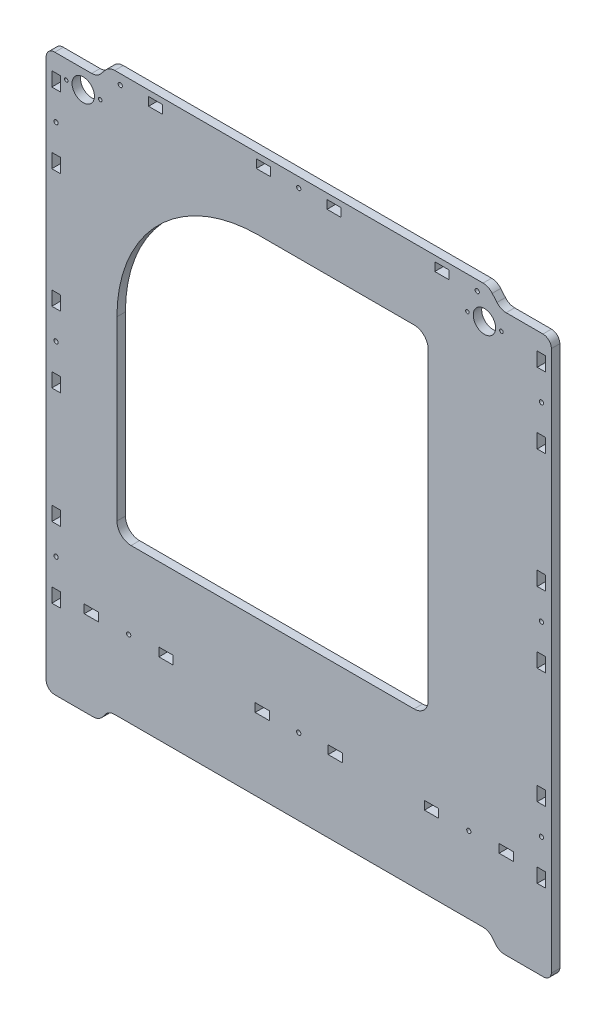
SolidWorks part; units mm, degrees
ref_plane "Спереди" through (0, 0, 0) normal (0, 0, 1) x (1, 0, 0)
ref_plane "Сверху" through (0, 0, 0) normal (0, 1, 0) x (1, 0, 0)
ref_plane "Справа" through (0, 0, 0) normal (1, 0, 0) x (0, 0, -1)
sketch "Эскиз1" plane through (0, 0, 0) normal (0, 0, 1) x (1, 0, 0)
  line L0 (146.8614, 191.5323) -> (172.8978, 191.5323)
  line L1 (-168.1958, 44.9723) -> (-168.1958, 34.9723)
  line L2 (174.8042, 34.9723) -> (168.8042, 34.9723)
  line L3 (178.8042, 185.543) -> (178.8042, -196.6758)
  line L4 (-178.1958, 185.543) -> (-178.1958, -195.7677)
  line L5 (172.8978, -201.7677) -> (145.8614, -201.7677)
  line L6 (-138.5545, -198.7314) -> (-136.2586, -195.7117)
  line L7 (-172.1022, -201.7677) -> (-145.0658, -201.7677)
  line L8 (-129.7473, -192.6754) -> (130.5428, -192.6754)
  line L9 (139.35, -198.7314) -> (137.0542, -195.7117)
  line L10 (174.8042, 179.1323) -> (174.8042, 169.359)
  line L11 (96.4442, 197.5323) -> (106.4199, 197.5323)
  line L12 (106.4199, 197.5323) -> (106.4442, 197.5149)
  line L13 (174.8042, 169.359) -> (174.8042, 169.1323)
  line L14 (137.0542, 198.496) -> (140.35, 194.5682)
  line L15 (130.5428, 201.5323) -> (-129.7473, 201.5323)
  line L16 (-136.2586, 198.4964) -> (-139.5545, 194.5686)
  line L17 (-146.0658, 191.5323) -> (-172.1022, 191.5323)
  line L18 (106.4199, 191.5323) -> (96.4442, 191.5323)
  line L19 (-168.1958, 34.9723) -> (-174.1958, 34.9723)
  line L20 (31.0942, -141.7677) -> (21.0942, -141.7677)
  line L21 (168.8042, 34.9723) -> (168.8042, 44.9723)
  line L22 (31.0942, -135.7677) -> (31.0942, -141.7677)
  line L23 (-30.4858, -135.7677) -> (-20.4858, -135.7677)
  line L24 (21.0942, -141.7677) -> (21.0942, -135.7677)
  line L25 (-20.4858, -141.7677) -> (-30.4858, -141.7677)
  line L26 (-20.4858, -135.7677) -> (-20.4858, -141.7677)
  line L27 (-168.1958, 179.1323) -> (-168.1958, 169.1323)
  line L28 (-30.4858, -141.7677) -> (-30.4858, -135.7677)
  line L29 (-174.1958, 34.9723) -> (-174.1958, 44.9723)
  line L30 (-174.1958, 44.9723) -> (-168.1958, 44.9723)
  line L31 (21.0942, -135.7677) -> (31.0942, -135.7677)
  line L32 (-174.1958, 179.1323) -> (-168.1958, 179.1323)
  line L33 (99.0942, -141.7677) -> (89.0942, -141.7677)
  line L34 (89.0942, -141.7677) -> (89.0942, -135.7677)
  line L35 (89.0942, -135.7677) -> (99.0942, -135.7677)
  line L36 (99.0942, -135.7677) -> (99.0942, -141.7677)
  line L37 (151.8942, -141.7677) -> (141.8942, -141.7677)
  line L38 (141.8942, -141.7677) -> (141.8942, -135.7677)
  line L39 (141.8942, -135.7677) -> (151.8942, -135.7677)
  line L40 (151.8942, -135.7677) -> (151.8942, -141.7677)
  line L41 (-19.6852, 191.5323) -> (-29.6852, 191.5323)
  line L42 (-29.6852, 191.5323) -> (-29.6864, 197.5323)
  line L43 (-29.6864, 197.5323) -> (-19.6864, 197.5323)
  line L44 (-19.6864, 197.5323) -> (-19.6852, 191.5323)
  line L45 (-174.1958, 119.1323) -> (-174.1958, 129.1323)
  line L46 (-141.2858, -135.7677) -> (-141.2858, -141.7677)
  line L47 (-151.2858, -135.7677) -> (-141.2858, -135.7677)
  line L48 (20.2942, 197.5323) -> (30.2942, 197.5323)
  line L49 (30.2942, 197.5323) -> (30.2942, 191.5323)
  line L50 (-141.2858, -141.7677) -> (-151.2858, -141.7677)
  line L51 (-174.1958, -5.0277) -> (-168.1958, -5.0277)
  line L52 (-174.1958, -15.0277) -> (-174.1958, -5.0277)
  line L53 (-174.1958, 169.1323) -> (-174.1958, 179.1323)
  line L54 (-168.1958, -5.0277) -> (-168.1958, -15.0277)
  line L55 (30.2942, 191.5323) -> (20.2942, 191.5323)
  line L56 (-151.2858, -141.7677) -> (-151.2858, -135.7677)
  line L57 (-168.1958, 119.1323) -> (-174.1958, 119.1323)
  line L58 (-168.1958, -15.0277) -> (-174.1958, -15.0277)
  line L59 (20.2942, 191.5323) -> (20.2942, 197.5323)
  line L60 (-168.1958, 169.1323) -> (-174.1958, 169.1323)
  line L61 (-174.1958, -86.7577) -> (-168.1958, -86.7577)
  line L62 (-174.1958, -96.7577) -> (-174.1958, -86.7577)
  line L63 (-168.1958, 129.1323) -> (-168.1958, 119.1323)
  line L64 (-174.1958, 129.1323) -> (-168.1958, 129.1323)
  line L65 (-174.1958, -136.7477) -> (-168.1958, -136.7477)
  line L66 (-174.1958, -146.7477) -> (-174.1958, -136.7477)
  line L67 (-98.4858, -141.7677) -> (-98.4858, -135.7677)
  line L68 (-98.4858, -135.7677) -> (-88.4858, -135.7677)
  line L69 (-88.4858, -135.7677) -> (-88.4858, -141.7677)
  line L70 (-168.1958, -146.7477) -> (-174.1958, -146.7477)
  line L71 (-168.1958, -136.7477) -> (-168.1958, -146.7477)
  line L72 (-168.1958, -96.7577) -> (-174.1958, -96.7577)
  line L73 (-168.1958, -86.7577) -> (-168.1958, -96.7577)
  line L74 (174.8042, -15.0277) -> (168.8042, -15.0277)
  line L75 (168.8042, -96.7577) -> (168.8042, -86.7577)
  line L76 (174.8042, -5.0277) -> (174.8042, -15.0277)
  line L77 (174.8042, -86.7577) -> (174.8042, -96.7577)
  line L78 (174.8042, -96.7577) -> (168.8042, -96.7577)
  line L79 (168.8042, -146.7477) -> (168.8042, -136.7477)
  line L80 (168.8042, -136.7477) -> (174.8042, -136.7477)
  line L81 (174.8042, -136.7477) -> (174.8042, -146.7477)
  line L82 (168.8042, -86.7577) -> (174.8042, -86.7577)
  line L83 (168.8042, 179.1323) -> (174.8042, 179.1323)
  line L84 (168.8042, 119.1323) -> (168.8042, 129.1323)
  line L85 (168.8042, 129.1323) -> (174.8042, 129.1323)
  line L86 (174.8042, 129.1323) -> (174.8042, 119.1323)
  line L87 (168.8042, 44.9723) -> (174.8042, 44.9723)
  line L88 (174.8042, 169.1323) -> (168.8042, 169.1323)
  line L89 (174.8042, 44.9723) -> (174.8042, 34.9723)
  line L90 (-95.8352, 191.5323) -> (-105.8352, 191.5323)
  line L91 (106.4442, 191.3325) -> (106.4199, 191.5323)
  line L92 (-105.8352, 191.5323) -> (-105.8364, 197.5323)
  line L93 (174.8042, 119.1323) -> (168.8042, 119.1323)
  line L94 (-105.8364, 197.5323) -> (-95.8364, 197.5323)
  line L95 (-95.8364, 197.5323) -> (-95.8352, 191.5323)
  line L96 (174.8042, -146.7477) -> (168.8042, -146.7477)
  line L97 (168.8042, 169.1323) -> (168.8042, 179.1323)
  line L98 (106.4442, 197.5149) -> (106.4442, 191.3325)
  line L99 (-88.4858, -141.7677) -> (-98.4858, -141.7677)
  line L100 (96.4442, 191.5323) -> (96.4442, 197.5323)
  line L101 (168.8042, -15.0277) -> (168.8042, -5.0277)
  line L102 (168.8042, -5.0277) -> (174.8042, -5.0277)
  line L103 (-158.5792, -141.7677) -> (201.8861, -141.7677) construction
  line L104 (-165.4171, 178.5323) -> (-136.2586, 178.5323) construction
  line L105 (112.0065, 178.5323) -> (153.0331, 178.5323) construction
  line L106 (-128.1958, -73.4677) -> (-128.1958, 51.5323)
  line L107 (-28.1958, 151.5323) -> (81.8042, 151.5323)
  line L108 (91.8042, 141.5323) -> (91.8042, -73.4677)
  line L109 (81.8042, -83.4677) -> (-118.1958, -83.4677)
  arc A0 (-172.1022, 191.5323) -> (-178.1958, 185.543) centre (-172.1958, 185.5331) ccw
  circle A1 centre (120.4942, -138.7677) radius 1.5
  circle A2 centre (0.3042, -138.7677) radius 1.5
  circle A3 centre (-119.8858, -138.7677) radius 1.5
  arc A4 (172.8978, -201.7677) -> (178.8042, -196.6758) centre (173.2588, -196.2149) ccw
  arc A5 (-129.7473, -192.6754) -> (-136.2586, -195.7117) centre (-129.7473, -201.1754) ccw
  arc A6 (139.35, -198.7314) -> (145.8614, -201.7677) centre (145.8614, -193.2677) ccw
  arc A7 (-145.0658, -201.7677) -> (-138.5545, -198.7314) centre (-145.0658, -193.2677) ccw
  arc A8 (-178.1958, -195.7677) -> (-172.1022, -201.7677) centre (-172.1958, -195.7684) ccw
  arc A9 (137.0542, -195.7117) -> (130.5428, -192.6754) centre (130.5428, -201.1754) ccw
  arc A10 (178.8042, 185.543) -> (172.8978, 191.5323) centre (172.8042, 185.5331) ccw
  arc A11 (137.0542, 198.496) -> (130.5428, 201.5323) centre (130.5428, 193.0323) ccw
  arc A12 (140.35, 194.5682) -> (146.8614, 191.5323) centre (146.861, 200.0323) ccw
  circle A13 centre (-171.1958, -116.7377) radius 1.5
  circle A14 centre (-171.1958, 14.9723) radius 1.5
  circle A15 centre (171.8042, 149.1323) radius 1.5
  circle A16 centre (126.4442, 194.5323) radius 1.5
  circle A17 centre (-151.9958, 178.5323) radius 7.9
  circle A18 centre (171.8042, -116.7377) radius 1.5
  circle A19 centre (171.8042, 14.9723) radius 1.5
  circle A20 centre (-171.1958, 149.1323) radius 1.5
  circle A21 centre (-125.8358, 194.5323) radius 1.5
  circle A22 centre (0.3042, 194.5444) radius 1.5
  circle A23 centre (131.5042, 178.5323) radius 7.9
  arc A24 (-129.7473, 201.5323) -> (-136.2586, 198.4964) centre (-129.7476, 193.0323) ccw
  arc A25 (-146.0658, 191.5323) -> (-139.5545, 194.5686) centre (-146.0658, 200.0323) ccw
  circle A26 centre (-139.9958, 178.5323) radius 1.25
  circle A27 centre (-163.9958, 178.5323) radius 1.25
  circle A28 centre (119.5042, 178.5323) radius 1.25
  circle A29 centre (143.5042, 178.5323) radius 1.25
  arc A30 (81.8042, 151.5323) -> (91.8042, 141.5323) centre (81.8042, 141.5323) cw
  arc A31 (91.8042, -73.4677) -> (81.8042, -83.4677) centre (81.8042, -73.4677) cw
  arc A32 (-118.1958, -83.4677) -> (-128.1958, -73.4677) centre (-118.1958, -73.4677) cw
  arc A33 (-128.1958, 51.5323) -> (-28.1958, 151.5323) centre (-28.1958, 51.5323) cw
  point P155 (-174.1958, 124.1323)
  point P156 (-171.1958, -146.7477)
  point P157 (106.4442, 194.4237)
  point P161 (31.0942, -138.7677)
  dimension "D119" = 2.5
  dimension "D120" = 2.5
  dimension "D121" = 12
  dimension "D122" = 12
  dimension "D123" = 2.5
  dimension "D124" = 2.5
  dimension "D125" = 12
  dimension "D126" = 12
  dimension "D1" = 357
  dimension "D2" = 403.3
  dimension "D3" = 403.3
  dimension "D4" = 23
  dimension "D5" = 26.2
  dimension "D6" = 4
  dimension "D7" = 10
  dimension "D8" = 22.4
  dimension "D9" = 10
  dimension "D10" = 7
  dimension "D11" = 20
  dimension "D12" = 20
  dimension "D13" = 10
  dimension "D14" = 74.16
  dimension "D15" = 4
  dimension "D16" = 6
  dimension "D17" = 6
  dimension "D18" = 10
  dimension "D19" = 4
  dimension "D20" = 20
  dimension "D21" = 20
  dimension "D22" = 10
  dimension "D23" = 7
  dimension "D24" = 4
  dimension "D25" = 71.73
  dimension "D26" = 4
  dimension "D27" = 10
  dimension "D28" = 19.98
  dimension "D29" = 7
  dimension "D30" = 20.01
  dimension "D31" = 10
  dimension "D32" = 55.02
  dimension "D33" = 4
  dimension "D34" = 23
  dimension "D35" = 47.3
  dimension "D36" = 10
  dimension "D37" = 12.4
  dimension "D38" = 10
  dimension "D39" = 20
  dimension "D40" = 20
  dimension "D41" = 10
  dimension "D42" = 74.16
  dimension "D43" = 10
  dimension "D44" = 6
  dimension "D45" = 6
  dimension "D46" = 6
  dimension "D47" = 6
  dimension "D48" = 6
  dimension "D49" = 4
  dimension "D50" = 7
  dimension "D51" = 4
  dimension "D52" = 6
  dimension "D53" = 6
  dimension "D54" = 4
  dimension "D55" = 20
  dimension "D56" = 20
  dimension "D57" = 7
  dimension "D58" = 4
  dimension "D59" = 6
  dimension "D60" = 71.73
  dimension "D61" = 4
  dimension "D62" = 6
  dimension "D63" = 7
  dimension "D64" = 19.98
  dimension "D65" = 20.01
  dimension "D66" = 10
  dimension "D67" = 6
  dimension "D68" = 4
  dimension "D69" = 55.02
  dimension "D70" = 7
  dimension "D71" = 4
  dimension "D72" = 4
  dimension "D73" = 4
  dimension "D74" = 7
  dimension "D75" = 4
  dimension "D76" = 6
  dimension "D77" = 10
  dimension "D78" = 6
  dimension "D79" = 10
  dimension "D80" = 10
  dimension "D81" = 6
  dimension "D82" = 6
  dimension "D83" = 10
  dimension "D84" = 52.36
  dimension "D85" = 20
  dimension "D86" = 66.15
  dimension "D87" = 178.5
  dimension "D88" = 19.99
  dimension "D89" = 52.36
  dimension "D90" = 20
  dimension "D91" = 66.15
  dimension "D92" = 19.99
  dimension "D93" = 6
  dimension "D94" = 10
  dimension "D95" = 3
  dimension "D96" = 6
  dimension "D97" = 10
  dimension "D98" = 16.91
  dimension "D99" = 21.4
  dimension "D100" = 21.4
  dimension "D101" = 6
  dimension "D102" = 10
  dimension "D103" = 58
  dimension "D104" = 6
  dimension "D105" = 60
  dimension "D106" = 10
  dimension "D107" = 3
  dimension "D108" = 6
  dimension "D109" = 10
  dimension "D110" = 58
  dimension "D111" = 16.91
  dimension "D112" = 10
  dimension "D113" = 6
  dimension "D114" = 3
  dimension "D115" = 21.4
  dimension "D116" = 21.4
  dimension "D117" = 178.5
  dimension "D118" = 178.5
  dimension "D127" = 50
  dimension "D128" = 50
extrude "Бобышка-Вытянуть1" add sketch "Эскиз1" along normal blind 6
